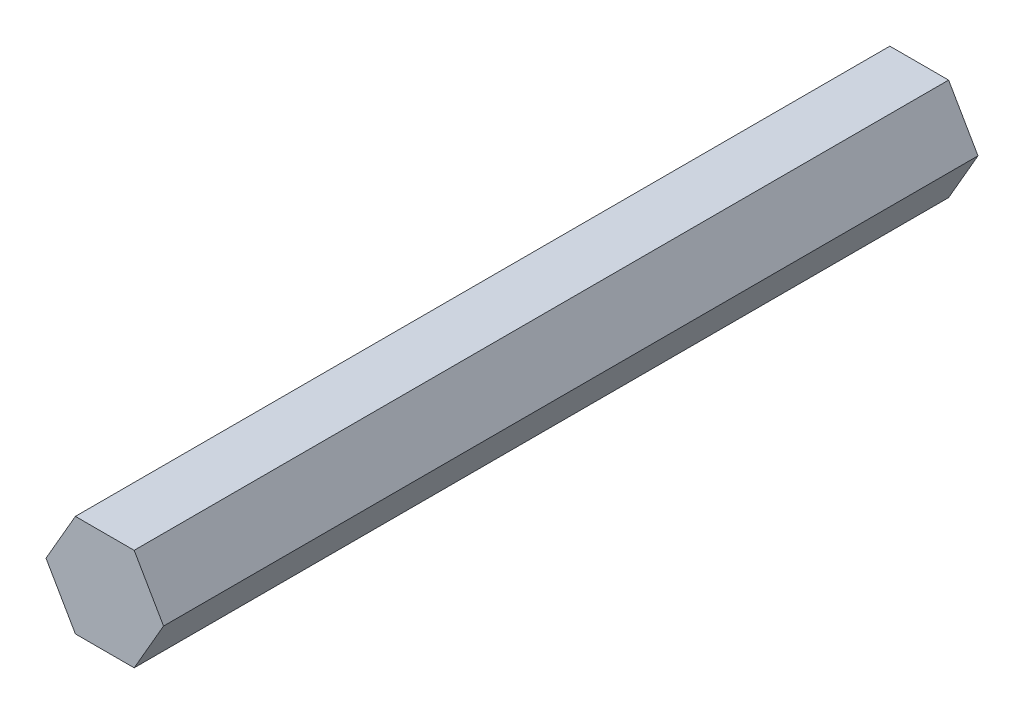
SolidWorks part; units mm, degrees
ref_plane "Front Plane" through (0, 0, 0) normal (0, 0, 1) x (1, 0, 0)
ref_plane "Top Plane" through (0, 0, 0) normal (0, 1, 0) x (1, 0, 0)
ref_plane "Right Plane" through (0, 0, 0) normal (1, 0, 0) x (0, 0, -1)
sketch "Sketch1" plane through (0, 0, 0) normal (0, 0, 1) x (1, 0, 0)
  line L1 (7.3323, 0) -> (3.6662, 6.35)
  line L2 (3.6662, 6.35) -> (-3.6662, 6.35)
  line L3 (-3.6662, 6.35) -> (-7.3323, 0)
  line L4 (-7.3323, 0) -> (-3.6662, -6.35)
  line L5 (-3.6662, -6.35) -> (3.6662, -6.35)
  line L6 (3.6662, -6.35) -> (7.3323, 0)
  circle A0 centre (0, 0) radius 6.35 construction
  dimension "D1" = 12.7
extrude "Boss-Extrude1" add sketch "Sketch1" along normal blind 101.6
